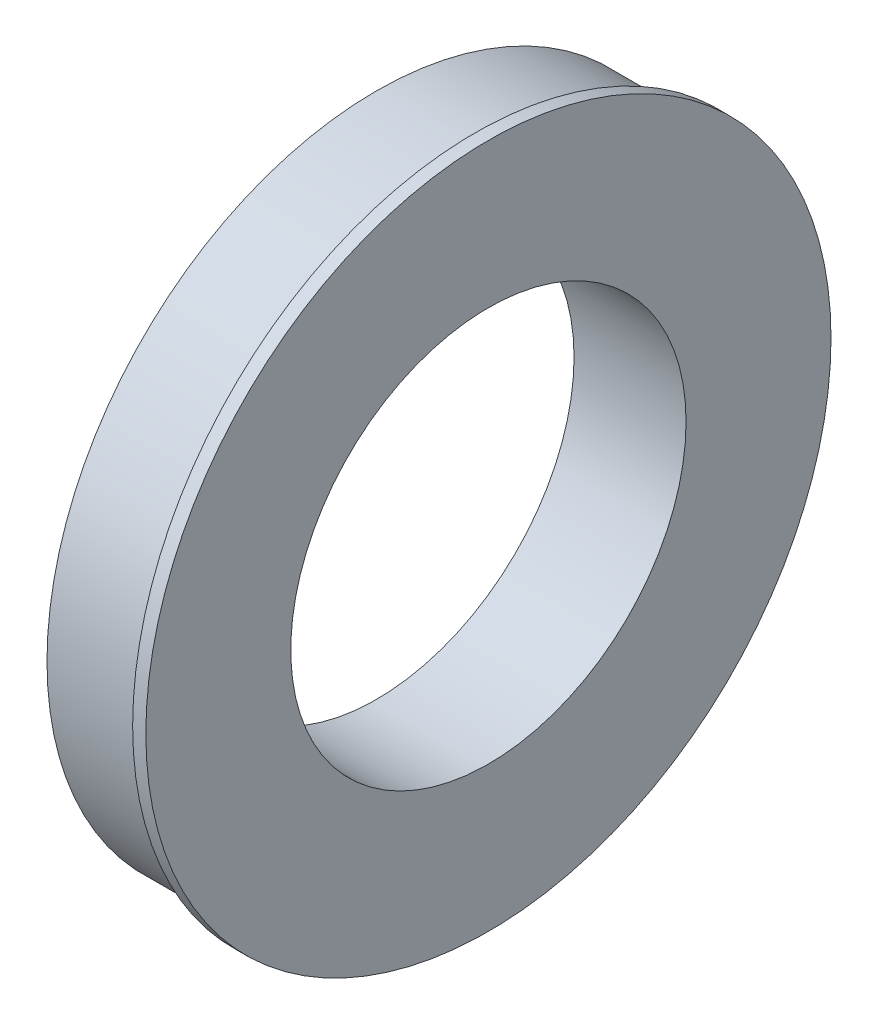
SolidWorks part; units mm, degrees
ref_plane "Front Plane" through (0, 0, 0) normal (0, 0, 1) x (1, 0, 0)
ref_plane "Top Plane" through (0, 0, 0) normal (0, 1, 0) x (1, 0, 0)
ref_plane "Right Plane" through (0, 0, 0) normal (1, 0, 0) x (0, 0, -1)
sketch "Sketch1" plane through (0, 0, 0) normal (1, 0, 0) x (0, 0, -1)
  circle A0 centre (0, 0) radius 38.1
  circle A1 centre (0, 0) radius 63.5
  dimension "D1" = 127
  dimension "D2" = 76.2
extrude "Boss-Extrude1" add sketch "Sketch1" along normal mid plane 19.05
sketch "Sketch2" plane through (9.525, 0, 0) normal (1, 0, 0) x (0, 0, -1)
  circle A0 centre (0, 0) radius 38.1 construction
  circle A1 centre (0, 0) radius 38.1
  circle A2 centre (0, 0) radius 66.04
  dimension "D1" = 132.08
extrude "Boss-Extrude2" add sketch "Sketch2" along normal blind 2.54
